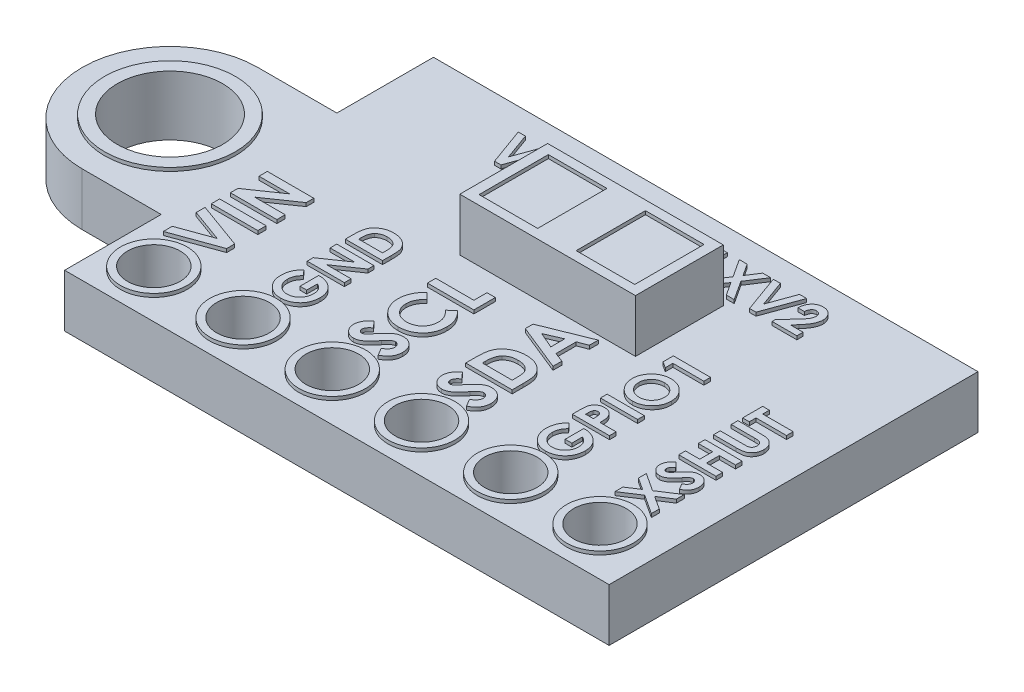
SolidWorks part; units mm, degrees
ref_plane "Ön Düzlem" through (0, 0, 0) normal (0, 0, 1) x (1, 0, 0)
ref_plane "Üst Düzlem" through (0, 0, 0) normal (0, 1, 0) x (1, 0, 0)
ref_plane "Sağ Düzlem" through (0, 0, 0) normal (1, 0, 0) x (0, 0, -1)
sketch "Çizim1" plane through (0, 0, 0) normal (0, 1, 0) x (1, 0, 0)
  line L0 (-10, 0) -> (10, 0) construction
  line L1 (-7.75, -5.25) -> (7.75, -5.25)
  line L2 (-7.75, -5.25) -> (-7.75, -2.5)
  line L3 (-7.75, 5.25) -> (7.75, 5.25)
  line L4 (7.75, -5.25) -> (7.75, -2.5)
  line L5 (-7.75, -5.25) -> (7.75, 5.25) construction
  line L6 (-7.75, 5.25) -> (7.75, -5.25) construction
  line L7 (-10, 2.5) -> (-7.75, 2.5)
  line L8 (-10, -2.5) -> (-7.75, -2.5)
  line L9 (10, -2.5) -> (7.75, -2.5)
  line L10 (10, 2.5) -> (7.75, 2.5)
  line L11 (-7.75, 2.5) -> (-7.75, 5.25)
  line L12 (7.75, 2.5) -> (7.75, 5.25)
  circle A0 centre (-10, 0) radius 1.5
  circle A1 centre (10, 0) radius 1.5
  arc A3 (-10, 2.5) -> (-10, -2.5) centre (-10, 0) ccw
  arc A4 (10, -2.5) -> (10, 2.5) centre (10, 0) ccw
  circle A5 centre (-10, 0) radius 2.5 construction
  circle A6 centre (10, 0) radius 2.5 construction
  point P0 (0, 0)
  dimension "D3" = 1
  dimension "D1" = 15.5
  dimension "D2" = 10.5
extrude "Yükseklik-Ekstrüzyon1" add sketch "Çizim1" along normal blind 1.5
sketch "Çizim2" plane through (0, 1.5, 0) normal (0, 1, 0) x (1, 0, 0)
  line L0 (0, 5.25) -> (0, 2) construction
  line L1 (7.75, 5.25) -> (-7.75, 5.25) construction
  line L3 (-2.5, 0.75) -> (2.5, 0.75)
  line L4 (-2.5, 0.75) -> (-2.5, 3.25)
  line L5 (-2.5, 3.25) -> (2.5, 3.25)
  line L6 (2.5, 0.75) -> (2.5, 3.25)
  line L7 (-2.5, 0.75) -> (2.5, 3.25) construction
  line L8 (-2.5, 3.25) -> (2.5, 0.75) construction
extrude "Yükseklik-Ekstrüzyon2" add sketch "Çizim2" along normal blind 1.5
sketch "Çizim3" plane through (0, 3, 0) normal (0, 1, 0) x (1, 0, 0)
  line L3 (0, 3.25) -> (0, 0.75) construction
  line L7 (2.5, 3.25) -> (-2.5, 3.25) construction
  line L12 (-2.5, 0.75) -> (2.5, 0.75) construction
  line L13 (0, 2) -> (-2.5, 2) construction
  line L14 (-2.5, 3.25) -> (-2.5, 0.75) construction
  line L15 (2.2157, 1.014) -> (0.548, 2.986) construction
  line L16 (-2.2157, 2.986) -> (-0.548, 2.986)
  line L17 (-2.2157, 2.986) -> (-2.2157, 1.014)
  line L18 (-2.2157, 1.014) -> (-0.548, 1.014)
  line L19 (-0.548, 2.986) -> (-0.548, 1.014)
  line L20 (-2.2157, 2.986) -> (-0.548, 1.014) construction
  line L21 (-2.2157, 1.014) -> (-0.548, 2.986) construction
  line L22 (2.2157, 2.986) -> (0.548, 1.014) construction
  line L23 (0.548, 2.986) -> (0.548, 1.014)
  line L24 (2.2157, 1.014) -> (0.548, 1.014)
  line L25 (2.2157, 2.986) -> (2.2157, 1.014)
  line L26 (2.2157, 2.986) -> (0.548, 2.986)
  point P10 (-1.3818, 2)
  point P19 (1.3818, 2)
extrude "Kes-Ekstrüzyon1" cut sketch "Çizim3" against normal blind 0.1
sketch "Çizim4" plane through (0, 1.5, 0) normal (0, 1, 0) x (1, 0, 0)
  line L0 (0, 0) -> (0, -1.1087) construction
  circle A1 centre (10, 0) radius 1.5 construction
  circle A3 centre (-10, 0) radius 1.5
  circle A4 centre (-10, 0) radius 1.8604
extrude "Yükseklik-Ekstrüzyon3" add sketch "Çizim4" along normal blind 0.1 and the other way blind 1.6
sketch "Çizim5" plane through (0, 1.5, 0) normal (0, 1, 0) x (1, 0, 0)
  line L0 (-7.75, -5.25) -> (-7.75, -3.98) construction
  line L1 (-7.75, -2.5) -> (-7.75, -5.25) construction
  line L2 (-7.75, -3.98) -> (-6.48, -3.98) construction
  circle A0 centre (-6.48, -3.98) radius 0.75
  circle A1 centre (-3.94, -3.98) radius 0.75
  circle A2 centre (-1.4, -3.98) radius 0.75
  circle A3 centre (1.14, -3.98) radius 0.75
  circle A4 centre (3.68, -3.98) radius 0.75
  circle A5 centre (6.22, -3.98) radius 0.75
  dimension "D1" = 6
extrude "Kes-Ekstrüzyon2" cut sketch "Çizim5" against normal blind 3.1
sketch "Çizim6" plane through (0, 1.5, 0) normal (0, 1, 0) x (1, 0, 0)
  circle A0 centre (-6.48, -3.98) radius 0.75 construction
  circle A1 centre (-6.48, -3.98) radius 0.75
  circle A2 centre (-6.48, -3.98) radius 0.95
  dimension "D1" = 0.2
extrude "Yükseklik-Ekstrüzyon4" add sketch "Çizim6" along normal blind 0.1 and the other way blind 1.6
pattern_linear "LÇoğaltma1" count 6 spacing 2.54 along (1, 0, 0) of "Yükseklik-Ekstrüzyon4"
sketch "Çizim7" plane through (0, 1.5, 0) normal (0, 1, 0) x (1, 0, 0)
  line L0 (-3.3625, -3.03) -> (-3.3625, 1.2923) construction
  line L1 (-5.8779, -3.03) -> (-5.8779, 1.2923) construction
  line L2 (-0.8471, -3.03) -> (-0.8471, 1.2923) construction
  line L3 (1.6682, -3.03) -> (1.6682, 1.2923) construction
  line L4 (4.1836, -3.03) -> (4.1836, 1.2923) construction
  line L5 (6.6989, -3.03) -> (6.6989, 1.2923) construction
  text T0 "VIN" font "Century Gothic" height in points 5
  text T1 "GND" font "Century Gothic" height in points 4
  text T2 "<b>SCL</b>" font "Century Gothic" height in points 5
  text T3 "SDA" font "Century Gothic" height in points 5
  text T4 "GPIO1" font "Century Gothic" height in points 4
  text T5 "<b>XSHUT</b>" font "Century Gothic" height in points 4
  dimension "D1" = 6
extrude "Yükseklik-Ekstrüzyon5" add sketch "Çizim7" along normal blind 0.1
sketch "Çizim8" plane through (0, 1.5, 0) normal (0, 1, 0) x (1, 0, 0)
  line L0 (-5.0829, 3.4564) -> (4.9171, 3.4564) construction
  line L1 (0, 0) -> (0, 5.25) construction
  line L2 (7.75, 5.25) -> (-7.75, 5.25) construction
  text T0 "VL53L0/1XV2" font "Century Gothic" height in points 4
extrude "Yükseklik-Ekstrüzyon6" add sketch "Çizim8" along normal blind 0.1
sketch "Çizim9" plane through (0, 0, 0) normal (0, -1, 0) x (1, 0, 0)
  line L0 (-1.7136, -3.2806) -> (-1.2276, -3.2806)
  line L1 (2.6326, 0.7695) -> (3.9286, 0.7695)
  line L2 (2.6326, 0.7695) -> (2.6326, -2.0656)
  line L3 (2.6326, -2.0656) -> (3.9286, -2.0656)
  line L4 (3.9286, 0.7695) -> (3.9286, -2.0656)
  line L5 (2.6326, 0.7695) -> (3.9286, -2.0656) construction
  line L6 (2.6326, -2.0656) -> (3.9286, 0.7695) construction
  line L7 (-2.7136, -3.2806) -> (-2.2276, -3.2806)
  line L8 (-2.7136, -3.2806) -> (-2.7136, -4.3336)
  line L9 (-2.7136, -4.3336) -> (-2.2276, -4.3336)
  line L10 (-2.2276, -3.2806) -> (-2.2276, -4.3336)
  line L11 (-2.7136, -3.2806) -> (-2.2276, -4.3336) construction
  line L12 (-2.7136, -4.3336) -> (-2.2276, -3.2806) construction
  line L17 (-1.7136, -3.2806) -> (-1.7136, -4.3336)
  line L18 (-1.7136, -4.3336) -> (-1.2276, -4.3336)
  line L23 (-1.2276, -3.2806) -> (-1.2276, -4.3336)
  line L24 (-1.7136, -3.2806) -> (-1.2276, -4.3336) construction
  line L25 (-1.7136, -4.3336) -> (-1.2276, -3.2806) construction
  line L26 (-0.7136, -3.2806) -> (-0.2276, -3.2806)
  line L27 (-0.7136, -3.2806) -> (-0.7136, -4.3336)
  line L28 (-0.7136, -4.3336) -> (-0.2276, -4.3336)
  line L29 (-0.2276, -3.2806) -> (-0.2276, -4.3336)
  line L30 (-0.7136, -3.2806) -> (-0.2276, -4.3336) construction
  line L31 (-0.7136, -4.3336) -> (-0.2276, -3.2806) construction
  line L32 (-5.7336, 1.0241) -> (-5.2741, 1.0241)
  line L33 (-6.7336, 1.0241) -> (-6.2741, 1.0241)
  line L34 (-6.7336, 1.0241) -> (-6.7336, -0.1705)
  line L35 (-6.7336, -0.1705) -> (-6.2741, -0.1705)
  line L36 (-6.2741, 1.0241) -> (-6.2741, -0.1705)
  line L37 (-6.7336, 1.0241) -> (-6.2741, -0.1705) construction
  line L38 (-6.7336, -0.1705) -> (-6.2741, 1.0241) construction
  line L39 (-5.7336, 1.0241) -> (-5.7336, -0.1705)
  line L40 (-5.7336, -0.1705) -> (-5.2741, -0.1705)
  line L41 (-5.2741, 1.0241) -> (-5.2741, -0.1705)
  line L42 (-5.7336, 1.0241) -> (-5.2741, -0.1705) construction
  line L43 (-5.7336, -0.1705) -> (-5.2741, 1.0241) construction
  point P0 (3.2806, -0.648)
  point P5 (-2.4706, -3.8071)
  point P10 (-6.5038, 0.4268)
  point P11 (-1.4706, -3.8071)
  point P16 (-0.4706, -3.8071)
  point P27 (-5.5038, 0.4268)
  dimension "D1" = 3
  dimension "D2" = 2
extrude "Yükseklik-Ekstrüzyon7" add sketch "Çizim9" along normal blind 1
sketch "Çizim10" plane through (0, -1, 0) normal (0, -1, 0) x (1, 0, 0)
  line L0 (-0.2276, -4.3336) -> (-0.2276, -3.2806) construction
  line L1 (-0.2276, -3.2806) -> (-0.7136, -3.2806) construction
  line L2 (-0.7136, -3.2806) -> (-0.7136, -4.3336) construction
  line L3 (-0.7136, -4.3336) -> (-0.2276, -4.3336) construction
  line L4 (-5.2741, -0.1705) -> (-5.2741, 1.0241)
  line L5 (-5.2741, 1.0241) -> (-5.7336, 1.0241)
  line L6 (-5.7336, 1.0241) -> (-5.7336, -0.1705)
  line L7 (-5.7336, -0.1705) -> (-5.2741, -0.1705)
  line L8 (-5.2741, -0.1705) -> (-5.2741, 1.0241)
  line L9 (-5.2741, 1.0241) -> (-5.7336, 1.0241)
  line L10 (-5.7336, 1.0241) -> (-5.7336, -0.1705)
  line L11 (-5.7336, -0.1705) -> (-5.2741, -0.1705)
  line L12 (-6.2741, -0.1705) -> (-6.2741, 1.0241)
  line L13 (-6.2741, 1.0241) -> (-6.7336, 1.0241)
  line L14 (-6.7336, 1.0241) -> (-6.7336, -0.1705)
  line L15 (-6.7336, -0.1705) -> (-6.2741, -0.1705)
  line L16 (-6.2741, -0.1705) -> (-6.2741, 1.0241)
  line L17 (-6.2741, 1.0241) -> (-6.7336, 1.0241)
  line L18 (-6.7336, 1.0241) -> (-6.7336, -0.1705)
  line L19 (-6.7336, -0.1705) -> (-6.2741, -0.1705)
  line L20 (-1.2276, -4.3336) -> (-1.2276, -3.2806) construction
  line L21 (-1.2276, -3.2806) -> (-1.7136, -3.2806) construction
  line L22 (-1.7136, -3.2806) -> (-1.7136, -4.3336) construction
  line L23 (-1.7136, -4.3336) -> (-1.2276, -4.3336) construction
  line L24 (-2.2276, -4.3336) -> (-2.2276, -3.2806) construction
  line L25 (-2.2276, -3.2806) -> (-2.7136, -3.2806) construction
  line L26 (-2.7136, -3.2806) -> (-2.7136, -4.3336) construction
  line L27 (-2.7136, -4.3336) -> (-2.2276, -4.3336) construction
  line L28 (-0.2276, -4.3336) -> (-0.2276, -3.2806)
  line L29 (-0.2276, -3.2806) -> (-0.7136, -3.2806)
  line L30 (-0.7136, -3.2806) -> (-0.7136, -4.3336)
  line L31 (-0.7136, -4.3336) -> (-0.2276, -4.3336)
  line L32 (-1.2276, -4.3336) -> (-1.2276, -3.2806)
  line L33 (-1.2276, -3.2806) -> (-1.7136, -3.2806)
  line L34 (-1.7136, -3.2806) -> (-1.7136, -4.3336)
  line L35 (-1.7136, -4.3336) -> (-1.2276, -4.3336)
  line L36 (-2.2276, -4.3336) -> (-2.2276, -3.2806)
  line L37 (-2.2276, -3.2806) -> (-2.7136, -3.2806)
  line L38 (-2.7136, -3.2806) -> (-2.7136, -4.3336)
  line L39 (-2.7136, -4.3336) -> (-2.2276, -4.3336)
  dimension "D1" = 0
  dimension "D2" = 0
extrude "Kes-Ekstrüzyon3" cut sketch "Çizim10" against normal blind 0.5
sketch "Sketch1" plane through (0, 1.5, 0) normal (0, 1, 0) x (1, 0, 0)
  line L0 (7.75, -2.5) -> (10, -2.5) construction
  line L1 (7.75, 2.5) -> (12.75, 2.5)
  line L2 (7.75, 2.5) -> (7.75, -2.5)
  line L3 (7.75, -2.5) -> (12.75, -2.5)
  line L4 (12.75, 2.5) -> (12.75, -2.5)
  dimension "D1" = 5
extrude "Cut-Extrude1" cut sketch "Sketch1" against normal blind 10
